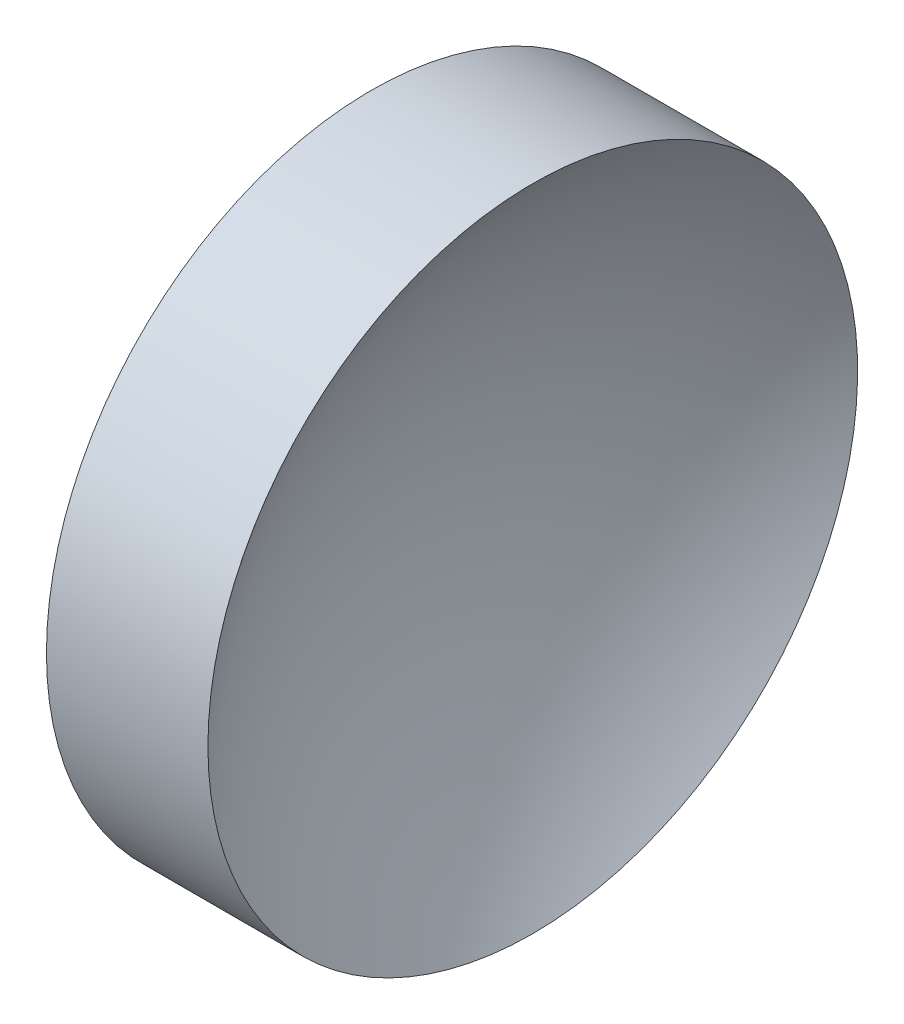
SolidWorks part; units mm, degrees
ref_plane "前视基准面" through (0, 0, 0) normal (0, 0, 1) x (1, 0, 0)
ref_plane "上视基准面" through (0, 0, 0) normal (0, 1, 0) x (1, 0, 0)
ref_plane "右视基准面" through (0, 0, 0) normal (1, 0, 0) x (0, 0, -1)
sketch "草图1" plane through (0, 0, 0) normal (0, 0, 1) x (1, 0, 0)
  line L0 (56.1009, 32.6108) -> (68.2773, 32.6108) construction
  line L1 (57.5323, 32.6108) -> (57.5323, 45.1108)
  line L2 (57.5323, 45.1108) -> (63.7454, 45.1108)
  line L3 (59.5323, 32.6108) -> (57.5323, 32.6108)
  arc A0 (63.7454, 45.1108) -> (59.5323, 32.6108) centre (80.1823, 32.6108) ccw
revolve "旋转1" add sketch "草图1" angle 360 about L0
